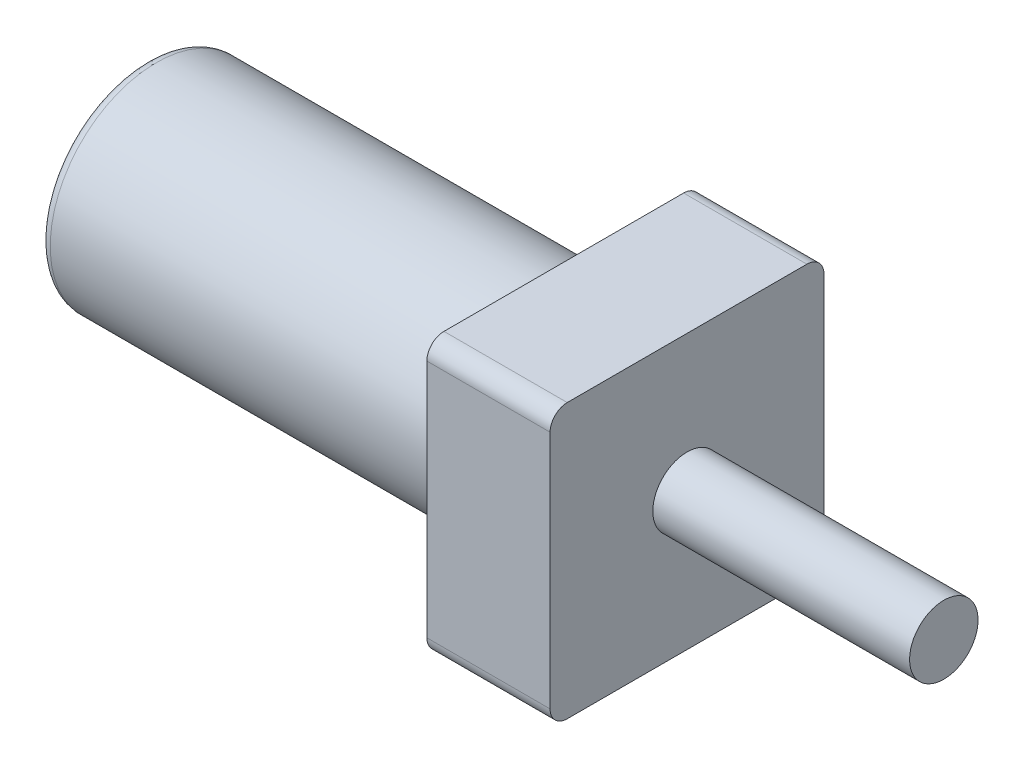
SolidWorks part; units mm, degrees
ref_plane "Front Plane" through (0, 0, 0) normal (0, 0, 1) x (1, 0, 0)
ref_plane "Top Plane" through (0, 0, 0) normal (0, 1, 0) x (1, 0, 0)
ref_plane "Right Plane" through (0, 0, 0) normal (1, 0, 0) x (0, 0, -1)
sketch "Sketch1" plane through (0, 0, 0) normal (0, 0, 1) x (1, 0, 0)
  line L0 (-49.7114, 0) -> (69.6686, 0) construction
  line L1 (0, 70.5757) -> (0, -79.6471) construction
  line L2 (154.94, 12.7) -> (295.91, 12.7)
  line L3 (0, 0) -> (295.91, 0)
  line L4 (0, 0) -> (0, 39.37)
  line L5 (0, 39.37) -> (154.94, 39.37)
  line L6 (154.94, 12.7) -> (154.94, 39.37)
  line L7 (295.91, 12.7) -> (295.91, 0)
  point P11 (141.4599, 0)
  dimension "D1" = 78.74
  dimension "D2" = 295.91
  dimension "D3" = 154.94
  dimension "D4" = 25.4
revolve "Revolve1" add sketch "Sketch1" angle 360 about L0
sketch "Sketch2" plane through (154.94, 0, 0) normal (1, 0, 0) x (0, 0, -1)
  line L0 (0, 71.138) -> (0, -74.4969) construction
  line L1 (-50.8, 50.8) -> (50.8, 50.8)
  line L2 (-50.8, 50.8) -> (-50.8, -50.8)
  line L3 (-50.8, -50.8) -> (50.8, -50.8)
  line L4 (50.8, 50.8) -> (50.8, -50.8)
  line L5 (-59.0217, 0) -> (78.4557, 0) construction
  dimension "D1" = 101.6
  dimension "D2" = 101.6
extrude "Boss-Extrude1" add sketch "Sketch2" along normal blind 45.72
fillet "Fillet1" radius 6.35 4 edges at (177.8, -50.8, 50.8) (177.8, -50.8, -50.8) (177.8, 50.8, -50.8) (177.8, 50.8, 50.8)
fillet "Fillet2" radius 3.81 1 edges at (0, 0, 39.37)
